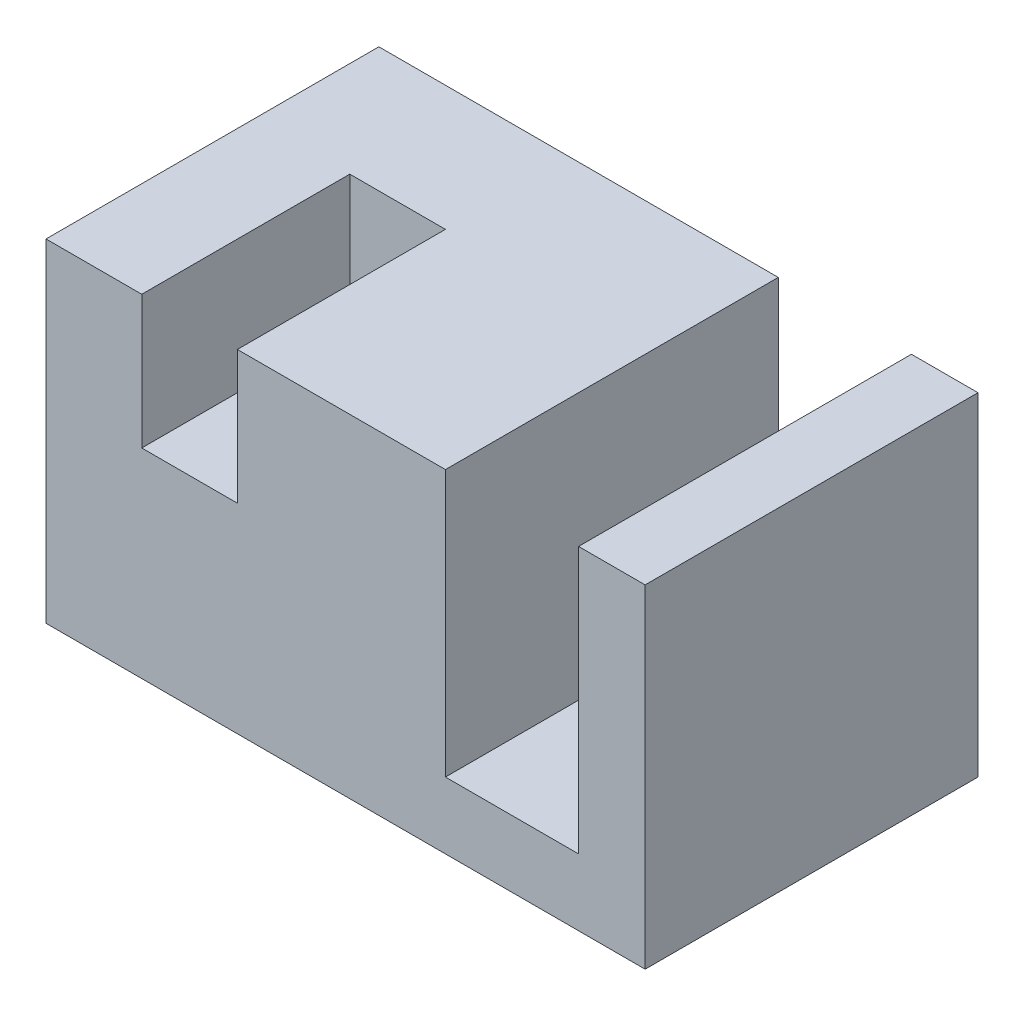
SolidWorks part; units mm, degrees
material "NEOPRENO"
ref_plane "Alzado" through (0, 0, 0) normal (0, 0, 1) x (1, 0, 0)
ref_plane "Planta" through (0, 0, 0) normal (0, 1, 0) x (1, 0, 0)
ref_plane "Vista lateral" through (0, 0, 0) normal (1, 0, 0) x (0, 0, -1)
sketch "Croquis1" plane through (0, 0, 0) normal (0, 1, 0) x (1, 0, 0)
  line L1 (-36, 20) -> (36, 20)
  line L2 (-36, 20) -> (-36, -20)
  line L3 (-36, -20) -> (36, -20)
  line L4 (36, 20) -> (36, -20)
  line L5 (-36, 20) -> (36, -20) construction
  line L6 (-36, -20) -> (36, 20) construction
  point P0 (0, 0)
  dimension "D1" = 40
  dimension "D2" = 72
extrude "Saliente-Extruir1" add sketch "Croquis1" along normal blind 40
sketch "Croquis5" plane through (0, 40, 0) normal (0, 1, 0) x (1, 0, 0)
  line L0 (-36, -20) -> (36, -20) construction
  line L1 (12, -20) -> (28, -20)
  line L2 (12, -20) -> (12, 20)
  line L3 (12, 20) -> (28, 20)
  line L4 (28, -20) -> (28, 20)
  line L5 (36, 20) -> (-36, 20) construction
  dimension "D1" = 16
  dimension "D2" = 8
extrude "Cortar-Extruir3" cut sketch "Croquis5" against normal blind 32
sketch "Croquis6" plane through (0, 40, 0) normal (0, 1, 0) x (1, 0, 0)
  line L0 (-36, -20) -> (12, -20) construction
  line L1 (-24.4925, -20) -> (-13, -20)
  line L2 (-24.4925, -20) -> (-24.4925, 5)
  line L3 (-24.4925, 5) -> (-13, 5)
  line L4 (-13, -20) -> (-13, 5)
  dimension "D1" = 25
  dimension "D2" = 25
extrude "Cortar-Extruir5" cut sketch "Croquis6" against normal blind 16
